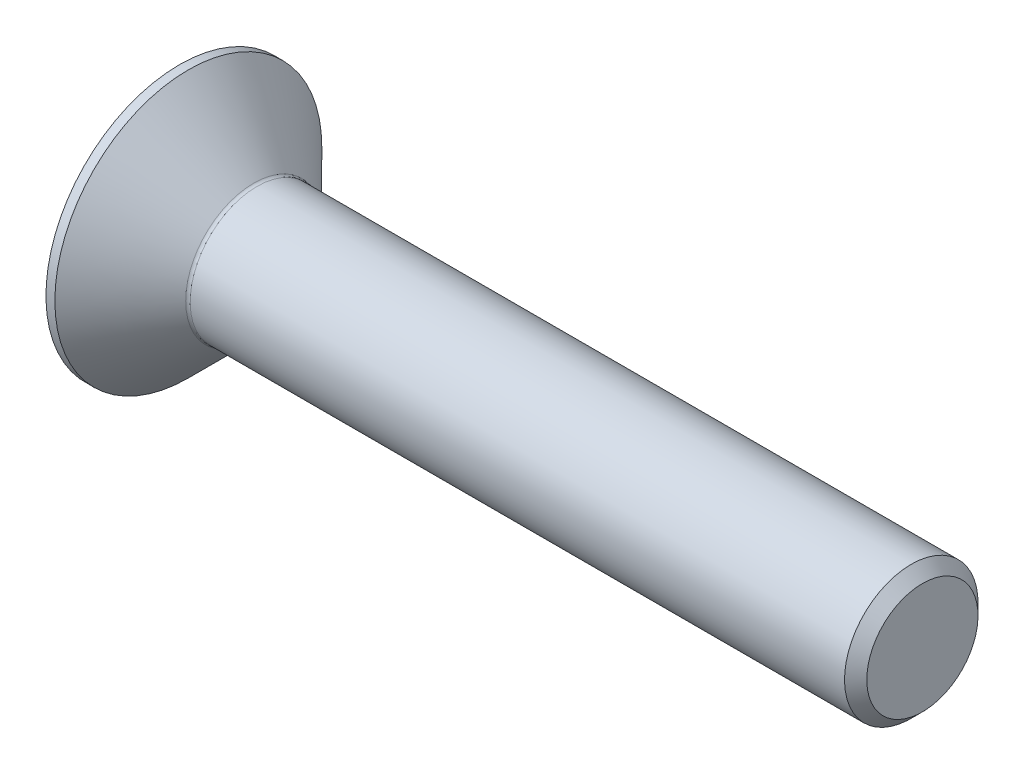
SolidWorks part; units mm, degrees
ref_plane "前基準面" through (0, 0, 0) normal (0, 0, 1) x (1, 0, 0)
ref_plane "上基準面" through (0, 0, 0) normal (0, 1, 0) x (1, 0, 0)
ref_plane "右基準面" through (0, 0, 0) normal (1, 0, 0) x (0, 0, -1)
sketch "草圖1" plane through (0, 0, 0) normal (0, 0, 1) x (1, 0, 0)
  line L0 (0, 3) -> (0, 0)
  line L1 (0, 0) -> (16.7, 0)
  line L2 (16.7, 0) -> (16.7, 1.5)
  line L3 (16.7, 1.5) -> (1.7, 1.5)
  line L4 (1.7, 1.5) -> (0.2, 3)
  line L5 (0.2, 3) -> (0, 3)
  line L6 (0, 0) -> (16.7, 0) construction
  point P6 (0, 0)
  dimension "D1" = 3
  dimension "D2" = 1.5
  dimension "D3" = 135
  dimension "D4" = 0.2
  dimension "D5" = 15
revolve "旋轉1" add sketch "草圖1" angle 360 about L6
sketch "草圖2" plane through (0, 0, 0) normal (-1, 0, 0) x (0, 0, 1)
  line L0 (-1, -0.5774) -> (0, -1.1547)
  line L1 (0, -1.1547) -> (1, -0.5774)
  line L2 (1, -0.5774) -> (1, 0.5774)
  line L3 (1, 0.5774) -> (0, 1.1547)
  line L4 (0, 1.1547) -> (-1, 0.5774)
  line L5 (-1, 0.5774) -> (-1, -0.5774)
extrude "除料-伸長1" cut sketch "草圖2" against normal blind 1.2
chamfer "導角1" distance 0.25 angle 45 1 edges at (16.7, 1.5, 0)
fillet "圓角1" radius 0.1 1 edges at (1.7, 1.5, 0)
